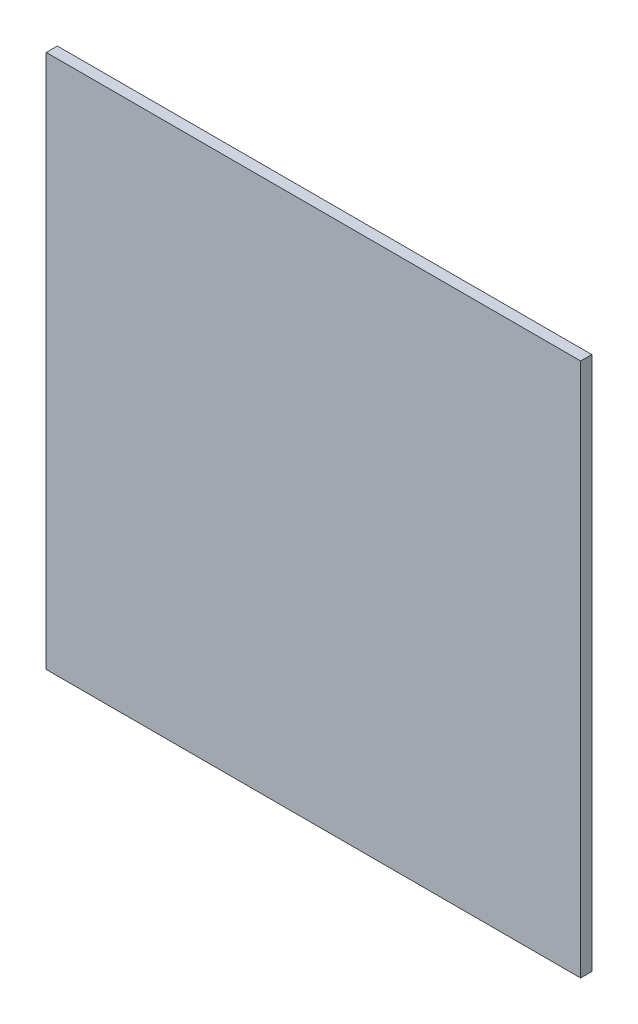
SolidWorks part; units mm, degrees
ref_plane "Front Plane" through (0, 0, 0) normal (0, 0, 1) x (1, 0, 0)
ref_plane "Top Plane" through (0, 0, 0) normal (0, 1, 0) x (1, 0, 0)
ref_plane "Right Plane" through (0, 0, 0) normal (1, 0, 0) x (0, 0, -1)
sketch "Sketch1" plane through (0, 0, 0) normal (0, 0, 1) x (1, 0, 0)
  line L1 (0, 0) -> (609.6, 0)
  line L2 (0, 0) -> (0, 609.6)
  line L3 (0, 609.6) -> (609.6, 609.6)
  line L4 (609.6, 0) -> (609.6, 609.6)
  dimension "D1" = 609.6
  dimension "D2" = 609.6
extrude "Boss-Extrude1" add sketch "Sketch1" along normal blind 12.7
